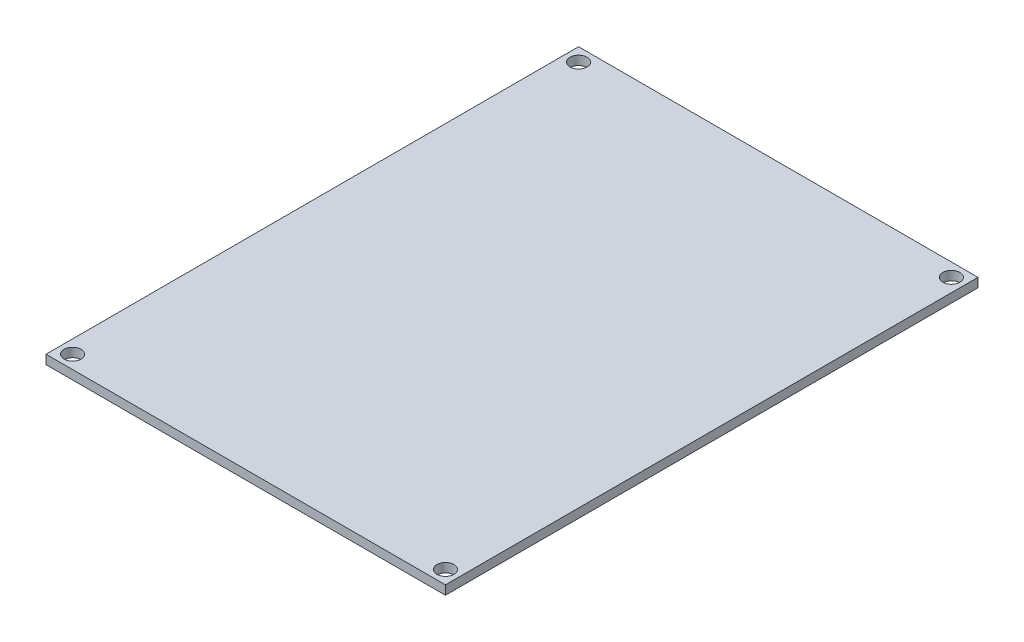
SolidWorks part; units mm, degrees
ref_plane "Front Plane" through (0, 0, 0) normal (0, 0, 1) x (1, 0, 0)
ref_plane "Top Plane" through (0, 0, 0) normal (0, 1, 0) x (1, 0, 0)
ref_plane "Right Plane" through (0, 0, 0) normal (1, 0, 0) x (0, 0, -1)
sketch "Sketch1" plane through (0, 0, 0) normal (0, 1, 0) x (1, 0, 0)
  line L1 (-37.5, -50) -> (37.5, -50)
  line L2 (-37.5, -50) -> (-37.5, 50)
  line L3 (-37.5, 50) -> (37.5, 50)
  line L4 (37.5, -50) -> (37.5, 50)
  line L5 (-37.5, -50) -> (37.5, 50) construction
  line L6 (-37.5, 50) -> (37.5, -50) construction
  point P0 (0, 0)
  dimension "D1" = 75
  dimension "D2" = 100
extrude "Boss-Extrude1" add sketch "Sketch1" along normal blind 1.7
sketch "Sketch2" plane through (0, 1.7, 0) normal (0, 1, 0) x (1, 0, 0)
  line L0 (0, 0) -> (0, 13.8685) construction
  line L1 (-35, -47.5) -> (35, -47.5)
  line L2 (-35, -47.5) -> (-35, 47.5)
  line L3 (-35, 47.5) -> (35, 47.5)
  line L4 (35, -47.5) -> (35, 47.5)
  line L5 (-35, -47.5) -> (35, 47.5) construction
  line L6 (-35, 47.5) -> (35, -47.5) construction
  circle A0 centre (-35, 47.5) radius 1.6
  circle A1 centre (-35, -47.5) radius 1.6
  circle A2 centre (35, -47.5) radius 1.6
  circle A3 centre (35, 47.5) radius 1.6
  point P0 (0, 0)
  dimension "D3" = 3.2
  dimension "D4" = 3.2
  dimension "D1" = 70
  dimension "D2" = 95
extrude "Cut-Extrude1" cut sketch "Sketch2" against normal up to next contours L3 A0 L2 | L2 A0 L3 | A3 L4 L3 | A3 L3 L4 | L2 A1 L1 | L1 A1 L2 | A2 L4 L1 | A2 L1 L4
